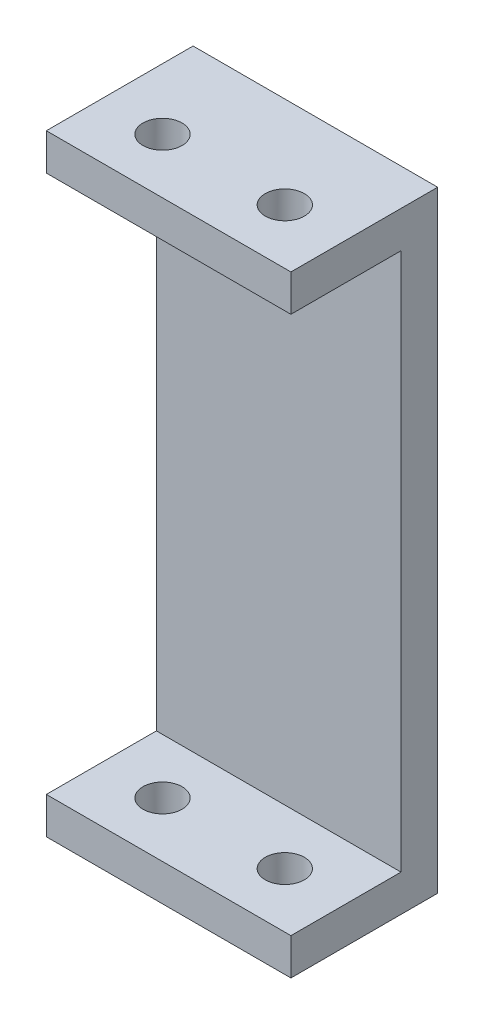
SolidWorks part; units mm, degrees
material "Thornel Mat VMA"
ref_plane "前视基准面" through (0, 0, 0) normal (0, 0, 1) x (1, 0, 0)
ref_plane "上视基准面" through (0, 0, 0) normal (0, 1, 0) x (1, 0, 0)
ref_plane "右视基准面" through (0, 0, 0) normal (1, 0, 0) x (0, 0, -1)
other "Configuration Table"
sketch "草图1" plane through (0, 0, 0) normal (0, 0, 1) x (1, 0, 0)
  line L1 (-15.8039, 24.0916) -> (4.1961, 24.0916)
  line L2 (-15.8039, 24.0916) -> (-15.8039, -25.9084)
  line L3 (-15.8039, -25.9084) -> (4.1961, -25.9084)
  line L4 (4.1961, 24.0916) -> (4.1961, -25.9084)
  dimension "D1" = 50
  dimension "D2" = 20
extrude "凸台-拉伸1" add sketch "草图1" along normal blind 12
sketch "草图2" plane through (0, 0, 12) normal (0, 0, 1) x (1, 0, 0)
  line L0 (-15.8039, 24.0916) -> (-15.8039, -25.9084) construction
  line L1 (-15.8039, 21.0916) -> (4.1961, 21.0916)
  line L2 (-15.8039, 21.0916) -> (-15.8039, -22.9084)
  line L3 (-15.8039, -22.9084) -> (4.1961, -22.9084)
  line L4 (4.1961, 21.0916) -> (4.1961, -22.9084)
  line L5 (4.1961, -25.9084) -> (4.1961, 24.0916) construction
  line L6 (4.1961, 24.0916) -> (-15.8039, 24.0916) construction
  line L7 (-15.8039, -25.9084) -> (4.1961, -25.9084) construction
  dimension "D1" = 3
  dimension "D2" = 3
extrude "切除-拉伸1" cut sketch "草图2" against normal blind 9 contours L2 L1 L4 L3
sketch "草图3" plane through (0, 24.0916, 0) normal (0, 1, 0) x (1, 0, 0)
  line L0 (-15.8039, -12) -> (-15.8039, 0) construction
  line L1 (-15.8039, -3) -> (4.1961, -3)
  line L2 (-15.8039, -3) -> (-15.8039, -12)
  line L3 (-15.8039, -12) -> (4.1961, -12)
  line L4 (4.1961, -3) -> (4.1961, -12)
  line L5 (4.1961, 0) -> (-15.8039, 0) construction
  line L6 (-15.8039, -7.5) -> (4.1961, -7.5) construction
  line L7 (-5.8039, -3) -> (-5.8039, -12) construction
  circle A0 centre (-10.8039, -7.5) radius 1.6
  circle A1 centre (-0.8039, -7.5) radius 1.6
  dimension "D2" = 10
  dimension "D3" = 3.2
  dimension "D1" = 3
  dimension "D4" = 5
extrude "切除-拉伸2" cut sketch "草图3" against normal through all contours A1 | A0
